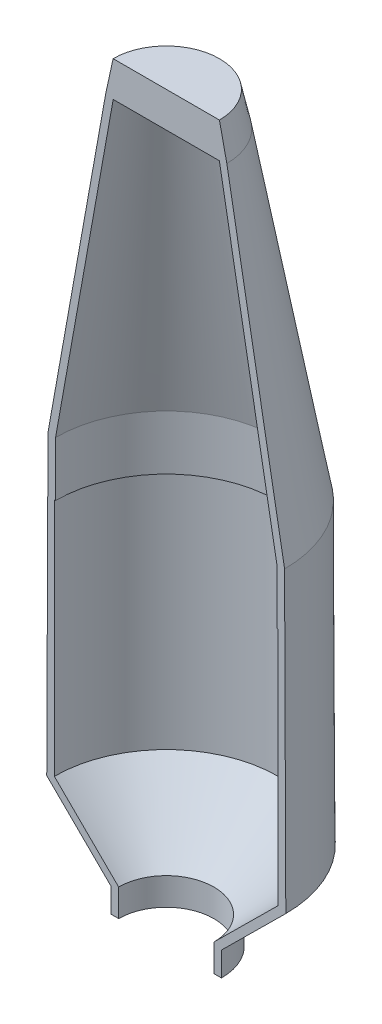
SolidWorks part; units mm, degrees
ref_plane "Front Plane" through (0, 0, 0) normal (0, 0, 1) x (1, 0, 0)
ref_plane "Top Plane" through (0, 0, 0) normal (0, 1, 0) x (1, 0, 0)
ref_plane "Right Plane" through (0, 0, 0) normal (1, 0, 0) x (0, 0, -1)
sketch "Sketch1" plane through (0, 0, 0) normal (1, 0, 0) x (0, 0, -1)
  line L0 (889, 5386.324) -> (1854.2, 0.0003)
  line L1 (1854.2, 0.0003) -> (1854.2, -914.3997)
  line L2 (1854.2, -914.3997) -> (1875.028, -914.3997)
  line L3 (1875.028, -914.3997) -> (1875.028, -4925.0597)
  line L4 (1875.028, -4925.0597) -> (797.687, -5991.8597)
  line L5 (797.687, -5991.8597) -> (797.687, -6450.5856)
  line L6 (1014.0088, 5408.7249) -> (1981.2, 11.2892)
  line L7 (1981.2, 11.2892) -> (2002.028, -4978.031)
  line L8 (889, 5386.324) -> (0, 5386.324)
  line L9 (0, 5386.324) -> (0, 6783.324)
  line L10 (2002.028, -4978.031) -> (924.687, -6044.831)
  line L11 (924.687, -6044.831) -> (924.687, -6450.5856)
  line L12 (1981.2, 11.2892) -> (1981.2, -787.3997) construction
  line L13 (1981.2, -787.3997) -> (2002.028, -787.3997) construction
  line L14 (2002.028, -787.3997) -> (2002.028, -4978.031) construction
  line L15 (797.687, -6450.5856) -> (924.687, -6450.5856)
  line L16 (1014.0088, 5408.7249) -> (797.687, 6403.5052)
  line L17 (0, 0) -> (0, 1746.8145) construction
  arc A0 (0, 6783.324) -> (797.687, 6403.5052) centre (236.0374, 6251.4928) cw
  dimension "D1" = 914.4
  dimension "D2" = 1854.2
  dimension "D3" = 889
  dimension "D4" = 5386.324
  dimension "D5" = 1875.028
  dimension "D6" = 4010.66
  dimension "D7" = 1066.8
  dimension "D8" = 797.687
  dimension "D10" = 1397
  dimension "D9" = 127
revolve "Revolve1" add sketch "Sketch1" angle 360 about L17
sketch "Sketch4" plane through (0, 0, 0) normal (1, 0, 0) x (0, 0, -1)
  line L0 (-2694.3628, 5977.1357) -> (-3046.021, 5977.1357)
  line L5 (7037.6144, 5977.1357) -> (0, 5977.1357)
  line L6 (7037.6144, 5977.1357) -> (7037.6144, 7002.5765)
  line L7 (7037.6144, 7002.5765) -> (-3046.021, 7002.5765)
  line L8 (-3046.021, 5977.1357) -> (-3046.021, 7002.5765)
  line L9 (0, -7682.3993) -> (-2694.3628, -7682.3993)
  line L10 (0, -7682.3993) -> (0, 5977.1357)
  line L12 (-2694.3628, -7682.3993) -> (-2694.3628, 5977.1357)
extrude "Extrude1" cut sketch "Sketch4" against normal mid plane 5080
